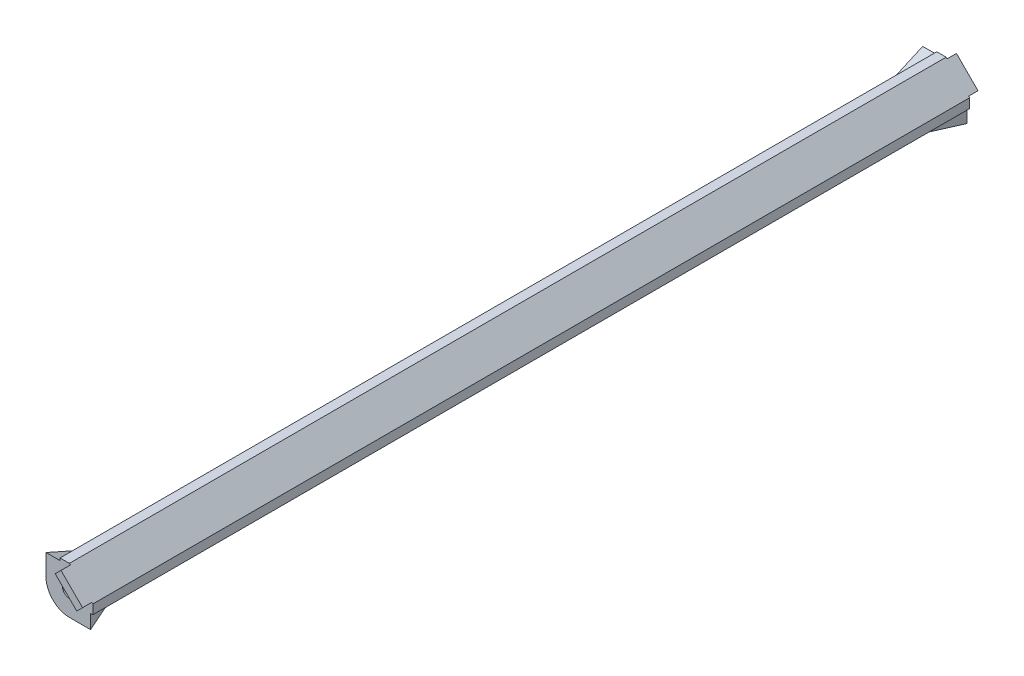
SolidWorks part; units mm, degrees
ref_plane "Front Plane" through (0, 0, 0) normal (0, 0, 1) x (1, 0, 0)
ref_plane "Top Plane" through (0, 0, 0) normal (0, 1, 0) x (1, 0, 0)
ref_plane "Right Plane" through (0, 0, 0) normal (1, 0, 0) x (0, 0, -1)
sketch "Sketch1" plane through (0, 0, 0) normal (0, 0, 1) x (1, 0, 0)
  line L0 (0, 0) -> (0, 5)
  line L3 (10, 0) -> (10, -5)
  line L6 (10, -5) -> (5, -5)
  line L8 (0, 5) -> (5, 5)
  line L9 (5, 5) -> (10, 0)
  arc A0 (5, -5) -> (0, 0) centre (5, 0) cw
  dimension "D1" = 10
  dimension "D2" = 5
  dimension "D3" = 5
extrude "Boss-Extrude1" add sketch "Sketch1" along normal blind 187
sketch "Sketch3" plane through (0, 0, 187) normal (0, 0, 1) x (1, 0, 0)
  line L0 (10, -5) -> (10, 0) construction
  line L1 (5, 5) -> (0, 5) construction
  circle A0 centre (5, 0) radius 1.5
  dimension "D1" = 3
  dimension "D2" = 5
  dimension "D3" = 5
extrude "Cut-Extrude2" cut sketch "Sketch3" against normal through all
sketch "Sketch2" plane through (0, 0, 0) normal (-1, 0, 0) x (0, 0, 1)
  line L1 (178, 0.5) -> (9, 0.5)
  line L3 (0, 5) -> (187, 5)
  line L4 (0, 5) -> (0, 4.5)
  line L5 (0, 5) -> (0, 0) construction
  line L6 (0, 4.5) -> (9, 0.5)
  line L7 (187, 5) -> (187, 4.5)
  line L8 (187, 5) -> (187, 0) construction
  line L9 (178, 0.5) -> (187, 4.5)
  dimension "D1" = 4.5
  dimension "D2" = 9
  dimension "D3" = 0.5
extrude "Cut-Extrude1" cut sketch "Sketch2" against normal blind 3
ref_plane "45deg-plane" through (2.5, -2.5, 0) normal (-0.7071, 0.7071, 0) x (0, 0, 1)
mirror "Mirror1" about plane through (2.5, -2.5, 0) normal (-0.7071, 0.7071, 0) of "Cut-Extrude1"
sketch "Sketch4" plane through (0, 0, 187) normal (0, 0, 1) x (1, 0, 0)
  line L5 (5.2019, 4.7981) -> (9.7981, 0.2019)
  line L6 (9.7981, 0.2019) -> (8.5607, -1.0355)
  line L7 (8.5607, -1.0355) -> (3.9645, 3.5607)
  line L8 (3.9645, 3.5607) -> (5.2019, 4.7981)
  line L9 (10, 0) -> (5, 5) construction
  point P6 (7.5, 2.5)
  point P7 (7.5, 2.5)
  dimension "D1" = 1.75
  dimension "D2" = 6.5
extrude "Boss-Extrude2" add sketch "Sketch4" along normal blind 2 and the other way offset from surface (189 mm away) 2 other way up to face at (6.5, 0, 0)
equation "\"beamDepth\"= 187mm"
equation "\"D1@Boss-Extrude1\"=\"beamDepth\""
